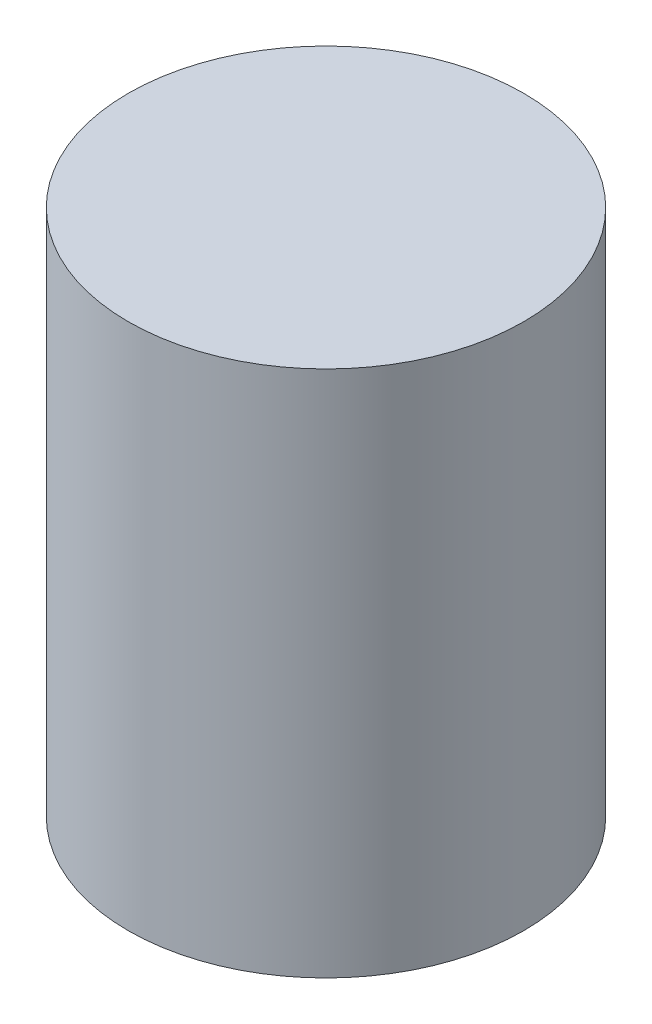
SolidWorks part; units mm, degrees
ref_plane "Front Plane" through (0, 0, 0) normal (0, 0, 1) x (1, 0, 0)
ref_plane "Top Plane" through (0, 0, 0) normal (0, 1, 0) x (1, 0, 0)
ref_plane "Right Plane" through (0, 0, 0) normal (1, 0, 0) x (0, 0, -1)
sketch "Sketch1" plane through (0, 0, 0) normal (0, 0, 1) x (1, 0, 0)
  line L0 (0, 0) -> (0, 4)
  dimension "D1" = 4
sweep "Sweep1" add path "Sketch1" circular profile diameter 3 parameters "D3"=3
